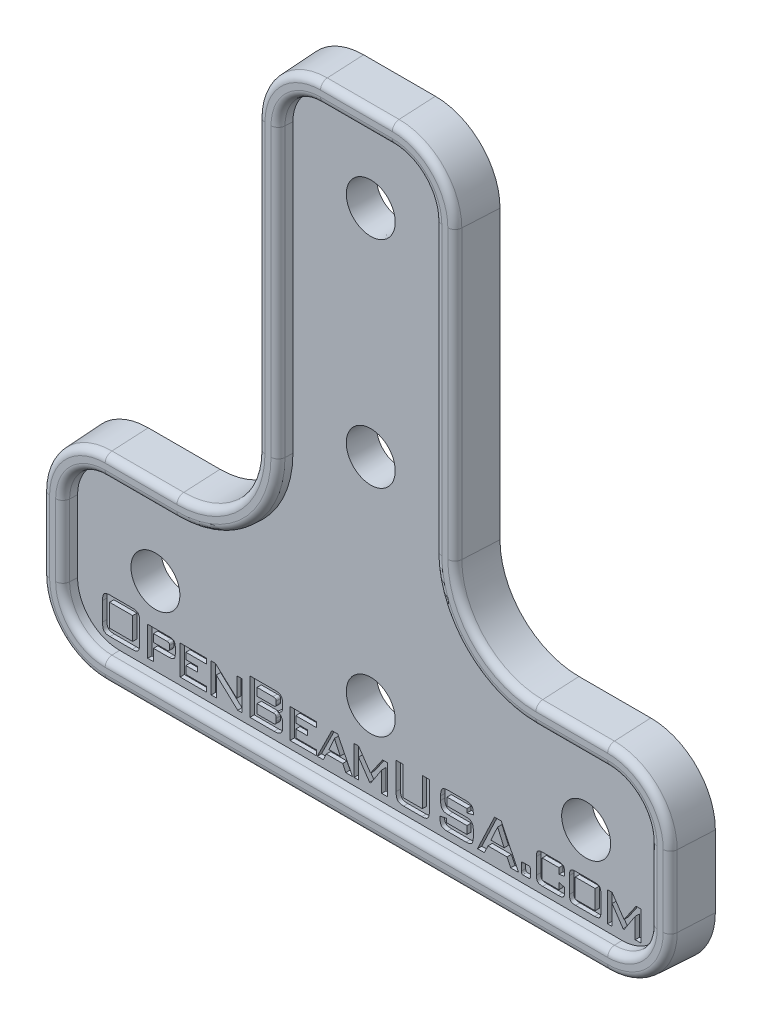
SolidWorks part; units mm, degrees
ref_plane "Front Plane" through (0, 0, 0) normal (0, 0, 1) x (1, 0, 0)
ref_plane "Top Plane" through (0, 0, 0) normal (0, 1, 0) x (1, 0, 0)
ref_plane "Right Plane" through (0, 0, 0) normal (1, 0, 0) x (0, 0, -1)
sketch "Sketch1" plane through (0, 0, 0) normal (0, 0, 1) x (1, 0, 0)
  line L0 (55, 0) -> (-55, 0) construction
  line L1 (-7.5, 30) -> (7.5, 30)
  line L2 (-7.5, 30) -> (-7.5, 0)
  line L3 (7.5, 0) -> (22.5, 0)
  line L4 (7.5, 30) -> (7.5, 0)
  line L5 (-22.5, 0) -> (-7.5, 0)
  line L6 (-22.5, 0) -> (-22.5, -15)
  line L7 (-22.5, -15) -> (22.5, -15)
  line L8 (22.5, 0) -> (22.5, -15)
  line L9 (0, 49.321) -> (0, -31.3726) construction
  line L10 (0, -54.6431) -> (0, 54.6431) construction
  dimension "D1" = 15
  dimension "D2" = 45
  dimension "D3" = 45
extrude "Boss-Extrude1" add sketch "Sketch1" along normal blind 2
fillet "Fillet1" radius 5 8 edges at (22.5, -15, 1) (22.5, 0, 1) (-7.5, 0, 1) (7.5, 0, 1) (7.5, 30, 1) (-22.5, -15, 1) (-22.5, 0, 1) (-7.5, 30, 1)
sketch "Sketch2" plane through (0, 0, 2) normal (0, 0, 1) x (1, 0, 0)
  line L0 (-22.5, -7.5) -> (22.5, -7.5) construction
  line L1 (-22.5, -5) -> (-22.5, -10) construction
  line L2 (22.5, -10) -> (22.5, -5) construction
  line L3 (0, 30) -> (0, -15) construction
  line L4 (2.5, 30) -> (-2.5, 30) construction
  line L5 (-17.5, -15) -> (17.5, -15) construction
  circle A0 centre (-15, -7.5) radius 1.6
  circle A1 centre (0, -7.5) radius 1.6
  circle A2 centre (15, -7.5) radius 1.6
  circle A3 centre (0, 22.5) radius 1.6
  circle A4 centre (0, 7.5) radius 1.6
  dimension "D1" = 3.2
  dimension "D2" = 15
  dimension "D3" = 15
  dimension "D4" = 15
  dimension "D5" = 15
extrude "Cut-Extrude1" cut sketch "Sketch2" against normal through all
other "Move Face1" face at (-9.4822, 1.9822, 1) face at (-15, 0, 1) face at (-20.5178, -1.9822, 1) face at (-22.5, -7.5, 1) face at (-20.5178, -13.0178, 1) face at (0, -15, 1) face at (20.5178, -13.0178, 1) face at (22.5, -7.5, 1) face at (20.5178, -1.9822, 1) face at (15, 0, 1) face at (9.4822, 1.9822, 1) face at (7.5, 15, 1) face at (5.5178, 28.0178, 1) face at (0, 30, 1) face at (-5.5178, 28.0178, 1) face at (-7.5, 15, 1) parameters "D1"=0.5
draft "Draft1" type of draft neutral plane draft angle 3 faces to draft 21 face at (16.6, -7.5, 0) face at (1.6, 22.5, 0) face at (1.6, 7.5, 0) face at (1.6, -7.5, 0) face at (-13.4, -7.5, 0) face at (-20.216, -2.284, 1) face at (-22, -7.5, 1) face at (-20.216, -12.716, 1) face at (0, -14.5, 1) face at (20.216, -12.716, 1) face at (22, -7.5, 1) face at (20.216, -2.284, 1) face at (15, -0.5, 1) face at (9.1805, 1.6805, 1) face at (7, 15, 1) face at (5.216, 27.716, 1) face at (0, 29.5, 1) face at (-5.216, 27.716, 1) face at (-7, 15, 1) face at (-9.1805, 1.6805, 1) face at (-15, -0.5, 1) neutral plane through (0, 0, 0) neutral plane normal (0, 0, -1) reverse direction yes parameters "D1"=3
sketch "Sketch4" plane through (0, 0, 2) normal (0, 0, 1) x (1, 0, 0)
  line L0 (-17.5, -12.9214) -> (17.5, -12.9214)
  line L1 (20.4214, -10) -> (20.4214, -5)
  line L2 (17.5, -2.0786) -> (12.5, -2.0786)
  line L3 (5.4214, 5) -> (5.4214, 25)
  line L4 (2.5, 27.9214) -> (-2.5, 27.9214)
  line L5 (-5.4214, 25) -> (-5.4214, 5)
  line L6 (-12.5, -2.0786) -> (-17.5, -2.0786)
  line L7 (-20.4214, -5) -> (-20.4214, -10)
  line L8 (-17.5, -14.3952) -> (17.5, -14.3952)
  line L9 (21.8952, -10) -> (21.8952, -5)
  line L10 (17.5, -0.6048) -> (12.5, -0.6048)
  line L11 (6.8952, 5) -> (6.8952, 25)
  line L12 (2.5, 29.3952) -> (-2.5, 29.3952)
  line L13 (-6.8952, 25) -> (-6.8952, 5)
  line L14 (-12.5, -0.6048) -> (-17.5, -0.6048)
  line L15 (-21.8952, -5) -> (-21.8952, -10)
  line L16 (-17.5, -14.3952) -> (17.5, -14.3952)
  line L17 (21.8952, -10) -> (21.8952, -5)
  line L18 (17.5, -0.6048) -> (12.5, -0.6048)
  line L19 (6.8952, 5) -> (6.8952, 25)
  line L20 (2.5, 29.3952) -> (-2.5, 29.3952)
  line L21 (-6.8952, 25) -> (-6.8952, 5)
  line L22 (-12.5, -0.6048) -> (-17.5, -0.6048)
  line L23 (-21.8952, -5) -> (-21.8952, -10)
  arc A2 (17.5, -12.9214) -> (20.4214, -10) centre (17.5, -10) ccw
  arc A3 (20.4214, -5) -> (17.5, -2.0786) centre (17.5, -5) ccw
  arc A4 (5.4214, 5) -> (12.5, -2.0786) centre (12.5, 5) ccw
  arc A5 (5.4214, 25) -> (2.5, 27.9214) centre (2.5, 25) ccw
  arc A6 (-2.5, 27.9214) -> (-5.4214, 25) centre (-2.5, 25) ccw
  arc A7 (-12.5, -2.0786) -> (-5.4214, 5) centre (-12.5, 5) ccw
  arc A8 (-17.5, -2.0786) -> (-20.4214, -5) centre (-17.5, -5) ccw
  arc A9 (-20.4214, -10) -> (-17.5, -12.9214) centre (-17.5, -10) ccw
  arc A10 (17.5, -14.3952) -> (21.8952, -10) centre (17.5, -10) ccw
  arc A11 (21.8952, -5) -> (17.5, -0.6048) centre (17.5, -5) ccw
  arc A12 (6.8952, 5) -> (12.5, -0.6048) centre (12.5, 5) ccw
  arc A13 (6.8952, 25) -> (2.5, 29.3952) centre (2.5, 25) ccw
  arc A14 (-2.5, 29.3952) -> (-6.8952, 25) centre (-2.5, 25) ccw
  arc A15 (-12.5, -0.6048) -> (-6.8952, 5) centre (-12.5, 5) ccw
  arc A16 (-17.5, -0.6048) -> (-21.8952, -5) centre (-17.5, -5) ccw
  arc A17 (-21.8952, -10) -> (-17.5, -14.3952) centre (-17.5, -10) ccw
  arc A18 (17.5, -14.3952) -> (21.8952, -10) centre (17.5, -10) ccw
  arc A19 (21.8952, -5) -> (17.5, -0.6048) centre (17.5, -5) ccw
  arc A20 (6.8952, 5) -> (12.5, -0.6048) centre (12.5, 5) ccw
  arc A21 (6.8952, 25) -> (2.5, 29.3952) centre (2.5, 25) ccw
  arc A22 (-2.5, 29.3952) -> (-6.8952, 25) centre (-2.5, 25) ccw
  arc A23 (-12.5, -0.6048) -> (-6.8952, 5) centre (-12.5, 5) ccw
  arc A24 (-17.5, -0.6048) -> (-21.8952, -5) centre (-17.5, -5) ccw
  arc A25 (-21.8952, -10) -> (-17.5, -14.3952) centre (-17.5, -10) ccw
  dimension "D1" = 0
extrude "Boss-Extrude3" add sketch "Sketch4" along normal blind 1 draft 3
fillet "Fillet3" radius 0.5 32 edges at (-7.5317, 0.0317, 3) (-5.4738, 15, 3) (-4.6028, 27.1028, 3) (0, 27.9738, 3) (4.6028, 27.1028, 3) (5.4738, 15, 3) (7.5317, 0.0317, 3) (15, -2.0262, 3) (19.6028, -2.8972, 3) (20.4738, -7.5, 3) (19.6028, -12.1028, 3) (0, -12.9738, 3) (-19.6028, -12.1028, 3) (-20.4738, -7.5, 3) (-19.6028, -2.8972, 3) (-8.4997, 0.9997, 3) (-6.8428, 15, 3) (-5.5708, 28.0708, 3) (0, 29.3428, 3) (5.5708, 28.0708, 3) (6.8428, 15, 3) (8.4997, 0.9997, 3) (15, -0.6572, 3) (20.5708, -1.9292, 3) (21.8428, -7.5, 3) (20.5708, -13.0708, 3) (0, -14.3428, 3) (-20.5708, -13.0708, 3) (-21.8428, -7.5, 3) (-20.5708, -1.9292, 3) (-15, -2.0262, 3) (-15, -0.6572, 3)
sketch "Sketch5" plane through (0, 0, 0) normal (0, 0, -1) x (-1, 0, 0)
  line L0 (0, 54.6431) -> (0, -54.6431) construction
  line L1 (-14.5, -13.8) -> (14.5, -13.8)
  line L2 (-15, -13.3) -> (-15, -10.3)
  line L3 (-14.5, -9.8) -> (14.5, -9.8)
  line L4 (15, -13.3) -> (15, -10.3)
  line L5 (-15, -13.8) -> (15, -9.8) construction
  line L6 (-15, -9.8) -> (15, -13.8) construction
  line L7 (17.5, -14.5) -> (-17.5, -14.5) construction
  arc A0 (14.5, -13.8) -> (15, -13.3) centre (14.5, -13.3) ccw
  arc A1 (14.5, -9.8) -> (15, -10.3) centre (14.5, -10.3) cw
  arc A2 (-14.5, -13.8) -> (-15, -13.3) centre (-14.5, -13.3) cw
  arc A3 (-15, -10.3) -> (-14.5, -9.8) centre (-14.5, -10.3) cw
  point P0 (0, -11.8)
  dimension "D4" = 0.5
  dimension "D1" = 30
  dimension "D2" = 4
  dimension "D3" = 0.7
extrude "Cut-Extrude2" cut sketch "Sketch5" against normal blind 0.2 draft 3
sketch "Sketch6" plane through (0, 0, 2) normal (0, 0, 1) x (1, 0, 0)
  line L0 (-19.1832, -12.4214) -> (19.1832, -12.4214) construction
  line L3 (-17.5, -12.9214) -> (17.5, -12.9214) construction
  arc A0 (17.5, -12.949) -> (20.449, -10) centre (17.5, -10) ccw construction
  arc A1 (-20.449, -10) -> (-17.5, -12.949) centre (-17.5, -10) ccw construction
  text T0 "OpenBeamUSA.com" font "BankGothic Md BT" height 2.5
  dimension "D1" = 0.5
extrude "Cut-Extrude3" cut sketch "Sketch6" against normal blind 0.3
